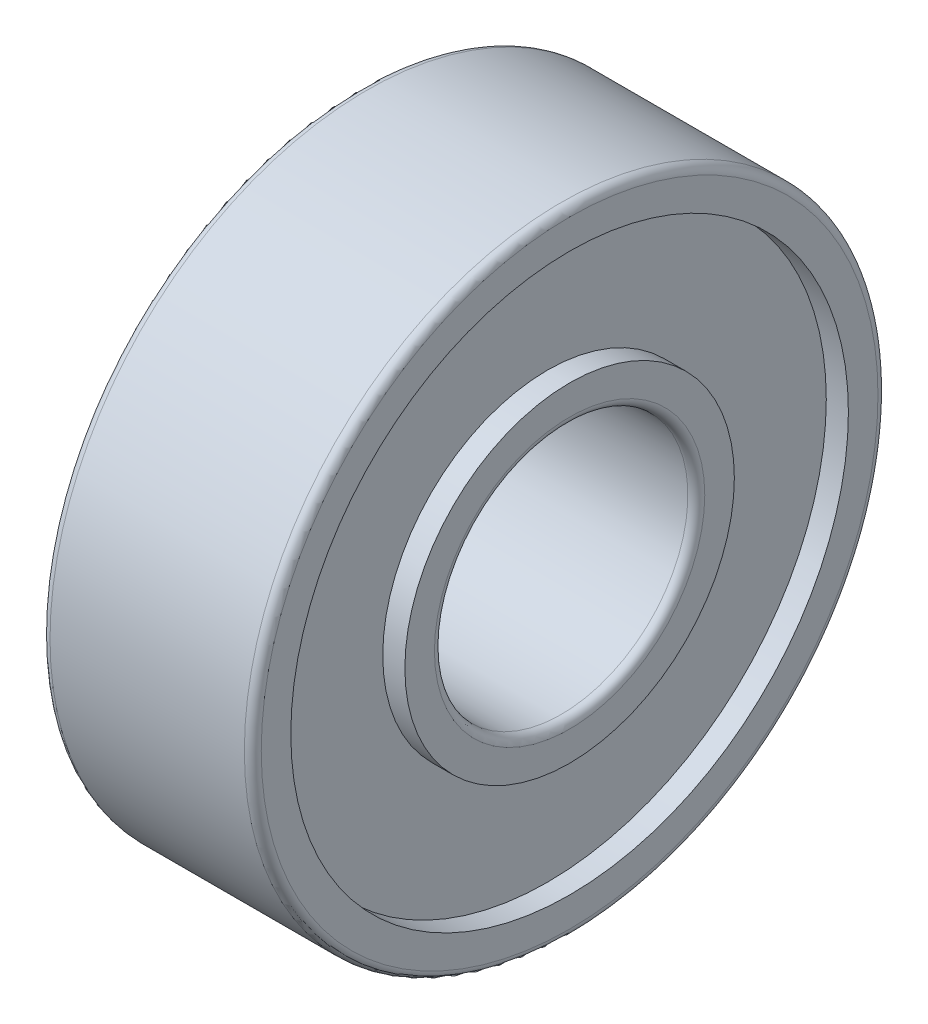
SolidWorks part; units mm, degrees
ref_plane "Front Plane" through (0, 0, 0) normal (0, 0, 1) x (1, 0, 0)
ref_plane "Top Plane" through (0, 0, 0) normal (0, 1, 0) x (1, 0, 0)
ref_plane "Right Plane" through (0, 0, 0) normal (1, 0, 0) x (0, 0, -1)
ref_plane "Plane1" through (0, 0, 0) normal (0, 0, 1) x (1, 0, 0)
sketch "Sketch1" plane through (0, 0, 0) normal (0, 0, 1) x (1, 0, 0)
  line L0 (0, 7.3) -> (0, 6.6)
  line L1 (0, 6.6) -> (0.5235, 6.6)
  line L2 (0.5235, 6.6) -> (0.5235, 3.9)
  line L3 (0.5235, 3.9) -> (0, 3.9)
  line L4 (0, 3.9) -> (0, 3.2)
  line L5 (0.2, 3) -> (4.8, 3)
  line L6 (5, 3.2) -> (5, 3.9)
  line L7 (5, 3.9) -> (4.4765, 3.9)
  line L8 (4.4765, 3.9) -> (4.4765, 6.6)
  line L9 (4.4765, 6.6) -> (5, 6.6)
  line L10 (5, 6.6) -> (5, 7.3)
  line L11 (4.8, 7.5) -> (0.2, 7.5)
  line L12 (4.8, 0) -> (0.2, 0) construction
  arc A0 (0, 3.2) -> (0.2, 3) centre (0.2, 3.2) ccw
  arc A1 (4.8, 3) -> (5, 3.2) centre (4.8, 3.2) ccw
  arc A2 (5, 7.3) -> (4.8, 7.5) centre (4.8, 7.3) ccw
  arc A3 (0.2, 7.5) -> (0, 7.3) centre (0.2, 7.3) ccw
revolve "Revolve1" add sketch "Sketch1" angle 360 about L12
